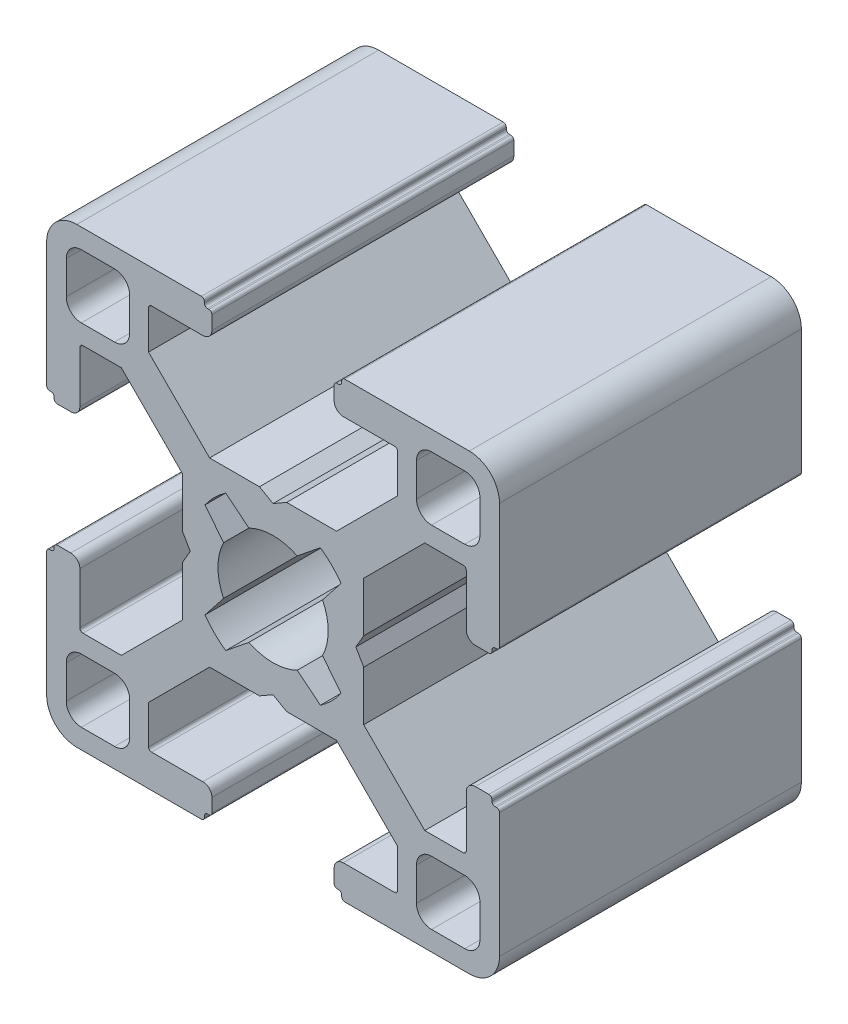
SolidWorks part; units mm, degrees
ref_plane "Płaszczyzna przednia" through (0, 0, 0) normal (0, 0, 1) x (1, 0, 0)
ref_plane "Płaszczyzna górna" through (0, 0, 0) normal (0, 1, 0) x (1, 0, 0)
ref_plane "Płaszczyzna prawa" through (0, 0, 0) normal (1, 0, 0) x (0, 0, -1)
sketch "Szkic1" plane through (0, 0, 0) normal (0, 0, 1) x (1, 0, 0)
  line L0 (109.26, 48.76) -> (107.06, 48.76)
  line L1 (106.06, 47.76) -> (106.06, 45.56)
  line L2 (107.06, 44.56) -> (109.26, 44.56)
  line L3 (110.26, 45.56) -> (110.26, 47.76)
  line L4 (94.9599, 38.3406) -> (93.4241, 39.5784)
  line L5 (92.0547, 38.2147) -> (93.2794, 36.6601)
  line L6 (93.2794, 33.4599) -> (92.0547, 31.9053)
  line L7 (93.4241, 30.5416) -> (94.9599, 31.7794)
  line L8 (98.1601, 31.7794) -> (99.6959, 30.5416)
  line L9 (101.0653, 31.9053) -> (99.8406, 33.4599)
  line L10 (99.8406, 36.6601) -> (101.0653, 38.2147)
  line L11 (99.6959, 39.5784) -> (98.1601, 38.3406)
  line L12 (83.86, 21.36) -> (86.06, 21.36)
  line L13 (87.06, 22.36) -> (87.06, 24.56)
  line L14 (86.06, 25.56) -> (83.86, 25.56)
  line L15 (82.86, 24.56) -> (82.86, 22.36)
  line L16 (110.26, 22.36) -> (110.26, 24.56)
  line L17 (109.26, 25.56) -> (107.06, 25.56)
  line L18 (106.06, 24.56) -> (106.06, 22.36)
  line L19 (86.06, 48.76) -> (83.86, 48.76)
  line L20 (82.86, 47.76) -> (82.86, 45.56)
  line L21 (83.86, 44.56) -> (86.06, 44.56)
  line L22 (87.06, 45.56) -> (87.06, 47.76)
  line L23 (107.06, 21.36) -> (109.26, 21.36)
  line L24 (96.56, 29.5751) -> (97.46, 29.06)
  line L25 (97.46, 29.06) -> (100.7645, 29.06)
  line L26 (100.7645, 29.06) -> (104.81, 25.01)
  line L27 (104.81, 25.01) -> (104.81, 22.46)
  line L28 (104.61, 22.26) -> (101.21, 22.26)
  line L29 (100.61, 21.66) -> (100.61, 20.76)
  line L30 (100.81, 20.56) -> (100.91, 20.56)
  line L31 (101.11, 20.36) -> (101.11, 20.26)
  line L32 (101.31, 20.06) -> (109.56, 20.06)
  line L33 (111.56, 22.06) -> (111.56, 30.31)
  line L34 (111.36, 30.51) -> (111.26, 30.51)
  line L35 (111.06, 30.71) -> (111.06, 30.81)
  line L36 (110.86, 31.01) -> (109.96, 31.01)
  line L37 (109.36, 30.41) -> (109.36, 27.01)
  line L38 (109.16, 26.81) -> (106.61, 26.81)
  line L39 (106.61, 26.81) -> (102.5645, 30.8555)
  line L40 (102.5645, 30.8555) -> (102.5645, 34.16)
  line L41 (102.5645, 34.16) -> (102.0449, 35.06)
  line L42 (102.0449, 35.06) -> (102.5645, 35.96)
  line L43 (102.5645, 35.96) -> (102.5645, 39.2645)
  line L44 (102.5645, 39.2645) -> (106.61, 43.31)
  line L45 (106.61, 43.31) -> (109.16, 43.31)
  line L46 (109.36, 43.11) -> (109.36, 39.71)
  line L47 (109.96, 39.11) -> (110.86, 39.11)
  line L48 (111.06, 39.31) -> (111.06, 39.41)
  line L49 (111.26, 39.61) -> (111.36, 39.61)
  line L50 (111.56, 39.81) -> (111.56, 48.06)
  line L51 (109.56, 50.06) -> (101.31, 50.06)
  line L52 (101.11, 49.86) -> (101.11, 49.76)
  line L53 (100.91, 49.56) -> (100.81, 49.56)
  line L54 (100.61, 49.36) -> (100.61, 48.46)
  line L55 (101.21, 47.86) -> (104.61, 47.86)
  line L56 (104.81, 47.66) -> (104.81, 45.11)
  line L57 (104.81, 45.11) -> (100.7645, 41.06)
  line L58 (100.7645, 41.06) -> (97.46, 41.06)
  line L59 (97.46, 41.06) -> (96.56, 40.5449)
  line L60 (96.56, 40.5449) -> (95.66, 41.06)
  line L61 (95.66, 41.06) -> (92.3555, 41.06)
  line L62 (92.3555, 41.06) -> (88.31, 45.11)
  line L63 (88.31, 45.11) -> (88.31, 47.66)
  line L64 (88.51, 47.86) -> (91.91, 47.86)
  line L65 (92.51, 48.46) -> (92.51, 49.36)
  line L66 (92.31, 49.56) -> (92.21, 49.56)
  line L67 (92.01, 49.76) -> (92.01, 49.86)
  line L68 (91.81, 50.06) -> (83.56, 50.06)
  line L69 (81.56, 48.06) -> (81.56, 39.81)
  line L70 (81.76, 39.61) -> (81.86, 39.61)
  line L71 (82.06, 39.41) -> (82.06, 39.31)
  line L72 (82.26, 39.11) -> (83.16, 39.11)
  line L73 (83.76, 39.71) -> (83.76, 43.11)
  line L74 (83.96, 43.31) -> (86.51, 43.31)
  line L75 (86.51, 43.31) -> (90.5555, 39.2645)
  line L76 (90.5555, 39.2645) -> (90.5555, 35.96)
  line L77 (90.5555, 35.96) -> (91.0751, 35.06)
  line L78 (91.0751, 35.06) -> (90.5555, 34.16)
  line L79 (90.5555, 34.16) -> (90.5555, 30.8555)
  line L80 (90.5555, 30.8555) -> (86.51, 26.81)
  line L81 (86.51, 26.81) -> (83.96, 26.81)
  line L82 (83.76, 27.01) -> (83.76, 30.41)
  line L83 (83.16, 31.01) -> (82.26, 31.01)
  line L84 (82.06, 30.81) -> (82.06, 30.71)
  line L85 (81.86, 30.51) -> (81.76, 30.51)
  line L86 (81.56, 30.31) -> (81.56, 22.06)
  line L87 (83.56, 20.06) -> (91.81, 20.06)
  line L88 (92.01, 20.26) -> (92.01, 20.36)
  line L89 (92.21, 20.56) -> (92.31, 20.56)
  line L90 (92.51, 20.76) -> (92.51, 21.66)
  line L91 (91.91, 22.26) -> (88.51, 22.26)
  line L92 (88.31, 22.46) -> (88.31, 25.01)
  line L93 (88.31, 25.01) -> (92.3555, 29.06)
  line L94 (92.3555, 29.06) -> (95.66, 29.06)
  line L95 (95.66, 29.06) -> (96.56, 29.5751)
  arc A0 (107.06, 48.76) -> (106.06, 47.76) centre (107.06, 47.76) ccw
  arc A1 (106.06, 45.56) -> (107.06, 44.56) centre (107.06, 45.56) ccw
  arc A2 (109.26, 44.56) -> (110.26, 45.56) centre (109.26, 45.56) ccw
  arc A3 (110.26, 47.76) -> (109.26, 48.76) centre (109.26, 47.76) ccw
  arc A4 (93.4241, 39.5784) -> (92.0547, 38.2147) centre (96.56, 35.06) ccw
  arc A5 (93.2794, 36.6601) -> (93.2794, 33.4599) centre (96.56, 35.06) ccw
  arc A6 (92.0547, 31.9053) -> (93.4241, 30.5416) centre (96.56, 35.06) ccw
  arc A7 (94.9599, 31.7794) -> (98.1601, 31.7794) centre (96.56, 35.06) ccw
  arc A8 (99.6959, 30.5416) -> (101.0653, 31.9053) centre (96.56, 35.06) ccw
  arc A9 (99.8406, 33.4599) -> (99.8406, 36.6601) centre (96.56, 35.06) ccw
  arc A10 (101.0653, 38.2147) -> (99.6959, 39.5784) centre (96.56, 35.06) ccw
  arc A11 (98.1601, 38.3406) -> (94.9599, 38.3406) centre (96.56, 35.06) ccw
  arc A12 (86.06, 21.36) -> (87.06, 22.36) centre (86.06, 22.36) ccw
  arc A13 (87.06, 24.56) -> (86.06, 25.56) centre (86.06, 24.56) ccw
  arc A14 (83.86, 25.56) -> (82.86, 24.56) centre (83.86, 24.56) ccw
  arc A15 (82.86, 22.36) -> (83.86, 21.36) centre (83.86, 22.36) ccw
  arc A16 (109.26, 21.36) -> (110.26, 22.36) centre (109.26, 22.36) ccw
  arc A17 (110.26, 24.56) -> (109.26, 25.56) centre (109.26, 24.56) ccw
  arc A18 (107.06, 25.56) -> (106.06, 24.56) centre (107.06, 24.56) ccw
  arc A19 (106.06, 22.36) -> (107.06, 21.36) centre (107.06, 22.36) ccw
  arc A20 (83.86, 48.76) -> (82.86, 47.76) centre (83.86, 47.76) ccw
  arc A21 (82.86, 45.56) -> (83.86, 44.56) centre (83.86, 45.56) ccw
  arc A22 (86.06, 44.56) -> (87.06, 45.56) centre (86.06, 45.56) ccw
  arc A23 (87.06, 47.76) -> (86.06, 48.76) centre (86.06, 47.76) ccw
  arc A24 (104.61, 22.26) -> (104.81, 22.46) centre (104.61, 22.46) ccw
  arc A25 (101.21, 22.26) -> (100.61, 21.66) centre (101.21, 21.66) ccw
  arc A26 (100.61, 20.76) -> (100.81, 20.56) centre (100.81, 20.76) ccw
  arc A27 (101.11, 20.36) -> (100.91, 20.56) centre (100.91, 20.36) ccw
  arc A28 (101.11, 20.26) -> (101.31, 20.06) centre (101.31, 20.26) ccw
  arc A29 (109.56, 20.06) -> (111.56, 22.06) centre (109.56, 22.06) ccw
  arc A30 (111.56, 30.31) -> (111.36, 30.51) centre (111.36, 30.31) ccw
  arc A31 (111.06, 30.71) -> (111.26, 30.51) centre (111.26, 30.71) ccw
  arc A32 (111.06, 30.81) -> (110.86, 31.01) centre (110.86, 30.81) ccw
  arc A33 (109.96, 31.01) -> (109.36, 30.41) centre (109.96, 30.41) ccw
  arc A34 (109.16, 26.81) -> (109.36, 27.01) centre (109.16, 27.01) ccw
  arc A35 (109.36, 43.11) -> (109.16, 43.31) centre (109.16, 43.11) ccw
  arc A36 (109.36, 39.71) -> (109.96, 39.11) centre (109.96, 39.71) ccw
  arc A37 (110.86, 39.11) -> (111.06, 39.31) centre (110.86, 39.31) ccw
  arc A38 (111.26, 39.61) -> (111.06, 39.41) centre (111.26, 39.41) ccw
  arc A39 (111.36, 39.61) -> (111.56, 39.81) centre (111.36, 39.81) ccw
  arc A40 (111.56, 48.06) -> (109.56, 50.06) centre (109.56, 48.06) ccw
  arc A41 (101.31, 50.06) -> (101.11, 49.86) centre (101.31, 49.86) ccw
  arc A42 (100.91, 49.56) -> (101.11, 49.76) centre (100.91, 49.76) ccw
  arc A43 (100.81, 49.56) -> (100.61, 49.36) centre (100.81, 49.36) ccw
  arc A44 (100.61, 48.46) -> (101.21, 47.86) centre (101.21, 48.46) ccw
  arc A45 (104.81, 47.66) -> (104.61, 47.86) centre (104.61, 47.66) ccw
  arc A46 (88.51, 47.86) -> (88.31, 47.66) centre (88.51, 47.66) ccw
  arc A47 (91.91, 47.86) -> (92.51, 48.46) centre (91.91, 48.46) ccw
  arc A48 (92.51, 49.36) -> (92.31, 49.56) centre (92.31, 49.36) ccw
  arc A49 (92.01, 49.76) -> (92.21, 49.56) centre (92.21, 49.76) ccw
  arc A50 (92.01, 49.86) -> (91.81, 50.06) centre (91.81, 49.86) ccw
  arc A51 (83.56, 50.06) -> (81.56, 48.06) centre (83.56, 48.06) ccw
  arc A52 (81.56, 39.81) -> (81.76, 39.61) centre (81.76, 39.81) ccw
  arc A53 (82.06, 39.41) -> (81.86, 39.61) centre (81.86, 39.41) ccw
  arc A54 (82.06, 39.31) -> (82.26, 39.11) centre (82.26, 39.31) ccw
  arc A55 (83.16, 39.11) -> (83.76, 39.71) centre (83.16, 39.71) ccw
  arc A56 (83.96, 43.31) -> (83.76, 43.11) centre (83.96, 43.11) ccw
  arc A57 (83.76, 27.01) -> (83.96, 26.81) centre (83.96, 27.01) ccw
  arc A58 (83.76, 30.41) -> (83.16, 31.01) centre (83.16, 30.41) ccw
  arc A59 (82.26, 31.01) -> (82.06, 30.81) centre (82.26, 30.81) ccw
  arc A60 (81.86, 30.51) -> (82.06, 30.71) centre (81.86, 30.71) ccw
  arc A61 (81.76, 30.51) -> (81.56, 30.31) centre (81.76, 30.31) ccw
  arc A62 (81.56, 22.06) -> (83.56, 20.06) centre (83.56, 22.06) ccw
  arc A63 (91.81, 20.06) -> (92.01, 20.26) centre (91.81, 20.26) ccw
  arc A64 (92.21, 20.56) -> (92.01, 20.36) centre (92.21, 20.36) ccw
  arc A65 (92.31, 20.56) -> (92.51, 20.76) centre (92.31, 20.76) ccw
  arc A66 (92.51, 21.66) -> (91.91, 22.26) centre (91.91, 21.66) ccw
  arc A67 (88.31, 22.46) -> (88.51, 22.26) centre (88.51, 22.46) ccw
  dimension "D1" = 3.65
  dimension "D2" = 30
  dimension "D3" = 30
  dimension "D4" = 8.1
extrude "Dodanie-wyciągnięcie1" add sketch "Szkic1" along normal blind 20
